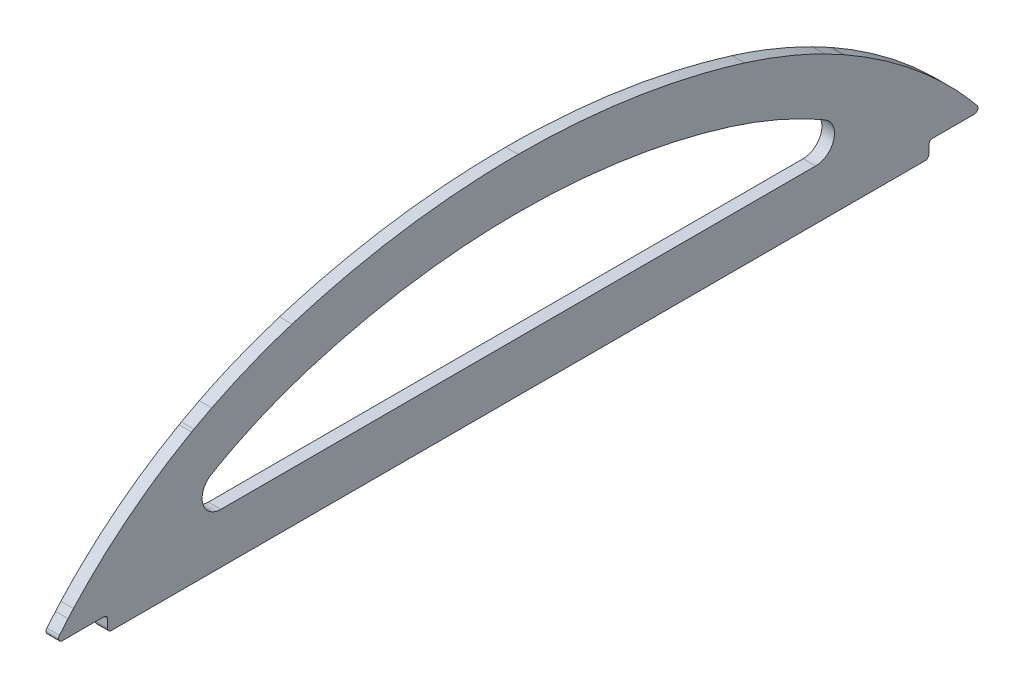
SolidWorks part; units mm, degrees
material "Plywood"
ref_plane "Front Plane" through (0, 0, 0) normal (0, 0, 1) x (1, 0, 0)
ref_plane "Top Plane" through (0, 0, 0) normal (0, 1, 0) x (1, 0, 0)
ref_plane "Right Plane" through (0, 0, 0) normal (1, 0, 0) x (0, 0, -1)
sketch "Sketch1" plane through (0, 0, 0) normal (1, 0, 0) x (0, 0, -1)
  line L0 (-96.2946, 5.9495) -> (96.2944, 5.9495)
  line L1 (-83.0866, 5.9495) -> (-83.0866, 9.1245)
  line L2 (-83.0866, 9.1245) -> (-93.8548, 9.1245)
  line L3 (83.0869, 5.9495) -> (83.0869, 9.1245)
  line L4 (83.0869, 9.1245) -> (93.8551, 9.1245)
  line L5 (72.5185, 16.1095) -> (-72.5187, 16.1095)
  spline S0 degree 3 poles (96.2944, 5.9495) (95.3162, 7.2776) (94.3159, 8.5664) (93.296, 9.8158) knots 0.775734 0.775734 0.775734 0.775734 1 1 1 1
  spline S1 degree 3 poles (93.296, 9.8158) (92.5735, 10.7008) (91.8374, 11.5701) (91.0886, 12.4237) knots 0 0 0 0 1 1 1 1
  spline S2 degree 3 poles (91.0886, 12.4237) (90.7324, 12.8297) (90.3692, 13.2365) (89.9993, 13.6442) knots 0 0 0 0 0.999999 0.999999 0.999999 0.999999
  spline S3 degree 3 poles (89.9993, 13.6442) (88.2637, 15.5574) (86.4569, 17.3838) (83.6563, 19.9929) (81.8777, 21.5829) (79.9594, 23.172) (79.0037, 23.9336) (78.8802, 24.0316) (78.8501, 24.0555) (74.7664, 27.2888) (70.4984, 30.1374) (66.0898, 32.6255) knots 0 0 0 0 0.25 0.25 0.375 0.484375 0.496094 0.496094 0.5 0.5 1 1 1 1
  spline S4 degree 3 poles (65.6328, 32.882) (64.439, 33.5479) (63.233, 34.1886) (62.0163, 34.8041) knots 0 0 0 0 0.18827 0.18827 0.18827 0.18827
  spline S5 degree 3 poles (66.0898, 32.6255) (65.9377, 32.7114) (65.7854, 32.7968) (65.6328, 32.882) knots 0 0 0 0 0.999999 0.999999 0.999999 0.999999
  spline S6 degree 3 poles (-96.2946, 5.9495) (-96.0496, 6.2797) (-95.5608, 6.9384) (-94.8141, 7.9117) (-94.0613, 8.8716) (-93.5507, 9.5017) (-93.2961, 9.8158) knots 0 0 0 0 0.252116 0.502813 0.752104 1 1 1 1
  spline S7 degree 3 poles (-93.2961, 9.8158) (-93.0545, 10.1097) (-92.5718, 10.6967) (-91.8358, 11.566) (-91.3376, 12.138) (-91.0888, 12.4237) knots 0 0 0 0 0.334016 0.667347 1 1 1 1
  spline S8 degree 3 poles (-91.0888, 12.4237) (-90.9093, 12.6273) (-90.5488, 13.0364) (-90.1831, 13.441) (-89.9995, 13.6442) knots 0 0 0 0 0.497638 1 1 1 1
  spline S9 degree 3 poles (-89.9995, 13.6442) (-89.7316, 13.9372) (-89.1963, 14.5227) (-88.3797, 15.3867) (-87.5543, 16.2391) (-86.7192, 17.0789) (-85.875, 17.9064) (-84.4559, 19.2626) (-82.7167, 20.8423) (-80.9328, 22.3643) (-79.7295, 23.3532) (-78.4521, 24.3773) (-76.7841, 25.6621) (-74.7061, 27.1763) (-72.5966, 28.6308) (-70.4569, 30.0242) (-68.2917, 31.3616) (-66.8231, 32.2047) (-66.09, 32.6255) knots 0 0 0 0 0.03885 0.077625 0.116327 0.154956 0.193513 0.232 0.347035 0.423377 0.461445 0.499444 0.583588 0.667444 0.751013 0.834295 0.917291 1 1 1 1
  spline S10 degree 3 poles (-66.09, 32.6255) (-65.9379, 32.7114) (-65.7855, 32.7968) (-65.6329, 32.882) knots 0 0 0 0 1 1 1 1
  spline S11 degree 3 poles (-65.6329, 32.882) (-65.3341, 33.0475) (-64.7366, 33.3786) (-63.8342, 33.8632) (-62.9282, 34.3396) (-62.3203, 34.6493) (-62.0164, 34.8041) knots 0 0 0 0 0.250232 0.500309 0.750231 1 1 1 1
  spline S12 degree 3 poles (-62.0164, 34.8041) (-61.1402, 35.2383) (-59.3888, 36.106) (-56.7181, 37.3111) (-54.0212, 38.445) (-51.2966, 39.499) (-48.5499, 40.4818) (-46.6986, 41.0723) (-45.7736, 41.3673) knots 0 0 0 0 0.167265 0.334295 0.501086 0.667635 0.83394 1 1 1 1
  spline S13 degree 3 poles (-45.7736, 41.3673) (-44.5402, 41.7394) (-42.0735, 42.4836) (-38.3385, 43.4787) (-34.5811, 44.385) (-30.8008, 45.1942) (-27.0006, 45.9085) (-23.1821, 46.5276) (-19.3476, 47.0516) (-15.4988, 47.4802) (-11.6376, 47.8142) (-7.7659, 48.0509) (-3.8856, 48.199) (-1.2957, 48.2167) (0, 48.2256) knots 0 0 0 0 0.083186 0.16637 0.249558 0.332759 0.415981 0.499234 0.582527 0.665873 0.749281 0.832764 0.916333 1 1 1 1
  spline S14 degree 3 poles (0, 48.2256) (1.2957, 48.2167) (3.8856, 48.199) (7.7659, 48.0509) (11.6376, 47.8142) (15.4987, 47.4802) (19.3475, 47.0516) (23.1821, 46.5276) (27.0005, 45.9085) (30.8007, 45.1941) (34.581, 44.385) (38.3384, 43.4787) (42.0734, 42.4836) (44.5401, 41.7394) (45.7734, 41.3673) knots 0 0 0 0 0.083667 0.167236 0.250719 0.334127 0.417473 0.500766 0.584019 0.667241 0.750442 0.83363 0.916814 1 1 1 1
  spline S15 degree 3 poles (45.7734, 41.3673) (46.6984, 41.0723) (48.5497, 40.4818) (51.2965, 39.499) (54.0211, 38.445) (56.718, 37.3111) (59.3887, 36.106) (61.14, 35.2383) (62.0163, 34.8041) knots 0 0 0 0 0.16606 0.332365 0.498914 0.665705 0.832735 1 1 1 1
  spline S26 degree 3 poles (-82.5005, 6.7892) (-82.2976, 7.0111) (-81.8761, 7.4722) (-81.3314, 8.054) (-80.7305, 8.6819) (-79.5477, 9.893) (-77.1002, 12.2713) (-74.3071, 14.695) (-71.6232, 16.8205) (-69.5673, 18.3671) (-67.4583, 19.8435) (-65.545, 21.1) (-64.3225, 21.8715) (-63.3625, 22.4571) (-62.6461, 22.8824) (-61.883, 23.3255) (-61.3348, 23.6402) (-61.0655, 23.7948) knots 0 0 0 0 0.03121 0.062421 0.093631 0.124842 0.249684 0.467905 0.530326 0.624209 0.749051 0.811472 0.873893 0.905103 0.936313 0.967524 0.998734 0.998734 0.998734 0.998734
  spline S27 degree 3 poles (-61.0655, 23.7948) (-61.0347, 23.8122) (-60.9732, 23.8468) (-60.8808, 23.8987) (-60.7883, 23.9505) (-60.7265, 23.9851) (-60.6956, 24.0023) knots 0.077726 0.077726 0.077726 0.077726 0.300433 0.523141 0.745848 0.968556 0.968556 0.968556 0.968556
  spline S28 degree 3 poles (-60.6956, 24.0023) (-60.5539, 24.0808) (-60.2624, 24.2422) (-59.7437, 24.5274) (-59.085, 24.8812) (-58.417, 25.2328) (-57.894, 25.5017) (-57.5985, 25.6524) (-57.4549, 25.7255) knots 0.003841 0.003841 0.003841 0.003841 0.126618 0.249395 0.494948 0.740501 0.863278 0.986054 0.986054 0.986054 0.986054
  spline S29 degree 3 poles (-57.4549, 25.7255) (-57.1384, 25.8823) (-56.4946, 26.2012) (-55.5903, 26.643) (-54.7306, 27.0521) (-53.5649, 27.5878) (-52.0522, 28.2524) (-50.2407, 29.007) (-48.4136, 29.722) (-46.8612, 30.2954) (-45.6454, 30.7221) (-44.7404, 31.0266) (-43.7827, 31.3379) (-43.0988, 31.5562) (-42.7624, 31.6635) knots 0.003251 0.003251 0.003251 0.003251 0.065263 0.127274 0.189286 0.251298 0.375321 0.499344 0.623367 0.74739 0.809401 0.871413 0.933424 0.995436 0.995436 0.995436 0.995436
  spline S30 degree 3 poles (-42.7624, 31.6635) (-42.3088, 31.8003) (-41.3911, 32.077) (-40.0755, 32.4668) (-38.8039, 32.8301) (-37.0888, 33.2976) (-34.8955, 33.8597) (-31.3915, 34.6916) (-26.9816, 35.6043) (-21.6471, 36.502) (-16.2801, 37.1998) (-11.79, 37.616) (-8.1875, 37.8477) (-5.921, 37.9544) (-4.1384, 38.0121) (-2.8096, 38.0395) (-1.4333, 38.0554) (-0.4743, 38.0621) (0, 38.0653) knots 0.001722 0.001722 0.001722 0.001722 0.032872 0.064021 0.095171 0.12632 0.188619 0.250918 0.375516 0.500113 0.624711 0.749309 0.811608 0.873907 0.905056 0.936206 0.967355 0.998505 0.998505 0.998505 0.998505
  spline S31 degree 3 poles (0, 38.0653) (0.4743, 38.0621) (1.4333, 38.0554) (2.8096, 38.0395) (4.1384, 38.0121) (5.9209, 37.9544) (8.1875, 37.8477) (11.7899, 37.616) (16.28, 37.1998) (21.6471, 36.502) (26.9815, 35.6043) (31.3914, 34.6916) (34.8954, 33.8597) (37.0887, 33.2976) (38.8037, 32.8301) (40.0754, 32.4668) (41.3909, 32.077) (42.3086, 31.8003) (42.7622, 31.6635) knots 0.001495 0.001495 0.001495 0.001495 0.032645 0.063794 0.094944 0.126093 0.188392 0.250691 0.375289 0.499887 0.624484 0.749082 0.811381 0.87368 0.90483 0.935979 0.967128 0.998278 0.998278 0.998278 0.998278
  spline S32 degree 3 poles (42.7622, 31.6635) (43.0989, 31.5561) (43.7833, 31.3376) (44.7417, 31.0261) (45.6473, 30.7213) (46.8641, 30.2943) (48.4178, 29.7204) (50.2461, 29.0048) (52.0591, 28.2494) (53.5729, 27.5841) (54.7391, 27.0481) (55.5998, 26.6384) (56.5052, 26.1958) (57.1498, 25.8766) (57.4668, 25.7195) knots 0.004564 0.004564 0.004564 0.004564 0.066624 0.128683 0.190743 0.252802 0.376922 0.501041 0.62516 0.749279 0.811339 0.873398 0.935458 0.997518 0.997518 0.997518 0.997518
  spline S33 degree 3 poles (57.4668, 25.7195) (57.7376, 25.5824) (58.2778, 25.3055) (59.0839, 24.882) (59.8859, 24.4504) (60.4176, 24.1573) (60.6828, 24.0094) knots 0.000025 0.000025 0.000025 0.000025 0.046559 0.093093 0.139626 0.18616 0.18616 0.18616 0.18616
  spline S34 degree 3 poles (60.6828, 24.0094) (60.7174, 23.9901) (60.7866, 23.9514) (60.8902, 23.8934) (60.9936, 23.8353) (61.0624, 23.7965) (61.0968, 23.7771) knots 0.001594 0.001594 0.001594 0.001594 0.250933 0.500272 0.749611 0.998951 0.998951 0.998951 0.998951
  spline S35 degree 3 poles (61.0968, 23.7771) (63.0869, 22.6538) (66.004, 20.858) (69.6507, 18.3105) (71.617, 16.8241) (72.9748, 15.7485) (73.9468, 14.9589) (75.5712, 13.5924) (78.5305, 10.9467) (80.9502, 8.4997) (82.4841, 6.8087) knots 0 0 0 0 0.249993 0.37499 0.484672 0.515921 0.562484 0.624983 0.749979 0.999972 0.999972 0.999972 0.999972
  dimension "D1" = 192.5891
  dimension "D2" = 3.175
  dimension "D3" = 13.208
  dimension "D5" = 10.16
extrude "Boss-Extrude1" add sketch "Sketch1" along normal blind 2.54
fillet "Fillet1" radius 3.81 2 edges at (1.27, 16.1095, -72.5185) (1.27, 16.1095, 72.5187)
fillet "Fillet2" radius 0.762 6 edges at (1.27, 5.9495, 83.0866) (1.27, 9.1245, 83.0866) (1.27, 9.1245, -83.0869) (1.27, 5.9495, -83.0869)
